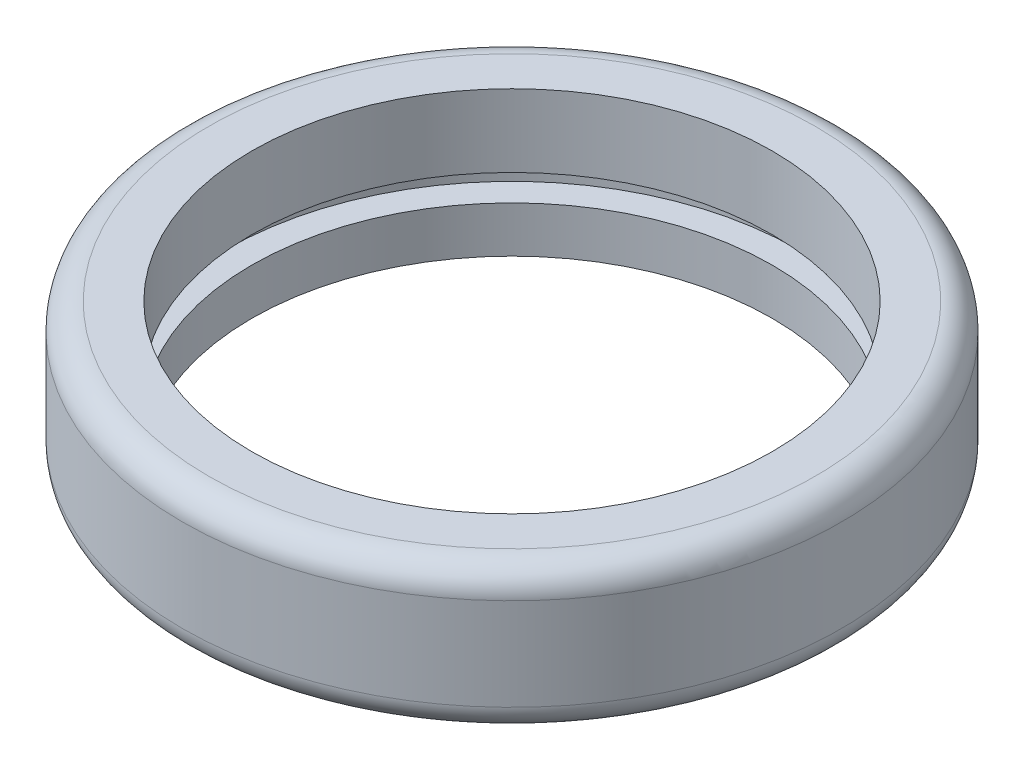
SolidWorks part; units mm, degrees
ref_plane "Ön Düzlem" through (0, 0, 0) normal (0, 0, 1) x (1, 0, 0)
ref_plane "Üst Düzlem" through (0, 0, 0) normal (0, 1, 0) x (1, 0, 0)
ref_plane "Sağ Düzlem" through (0, 0, 0) normal (1, 0, 0) x (0, 0, -1)
sketch "Sketch1" plane through (0, 0, 0) normal (0, 0, 1) x (1, 0, 0)
  line L0 (19.75, -5.5) -> (19.75, -2)
  line L1 (19.75, -2) -> (21.75, -2)
  line L2 (21.75, -2) -> (21.75, 0)
  line L3 (21.75, 0) -> (19.75, 0)
  line L4 (19.75, 0) -> (19.75, 5.5)
  line L5 (19.75, 5.5) -> (25, 5.5)
  line L6 (25, 5.5) -> (25, -5.5)
  line L7 (25, -5.5) -> (19.75, -5.5)
  line L8 (0, 0) -> (0, 50000) construction
  point P12 (25, 0)
  dimension "D1" = 25
  dimension "D2" = 5.25
  dimension "D3" = 2
  dimension "D4" = 2
  dimension "D5" = 11
  dimension "D6" = 5.5
revolve "Revolve1" add sketch "Sketch1" angle 360 about L8
fillet "Fillet1" radius 2 2 edges at (0, -5.5, -25) (0, 5.5, -25)
